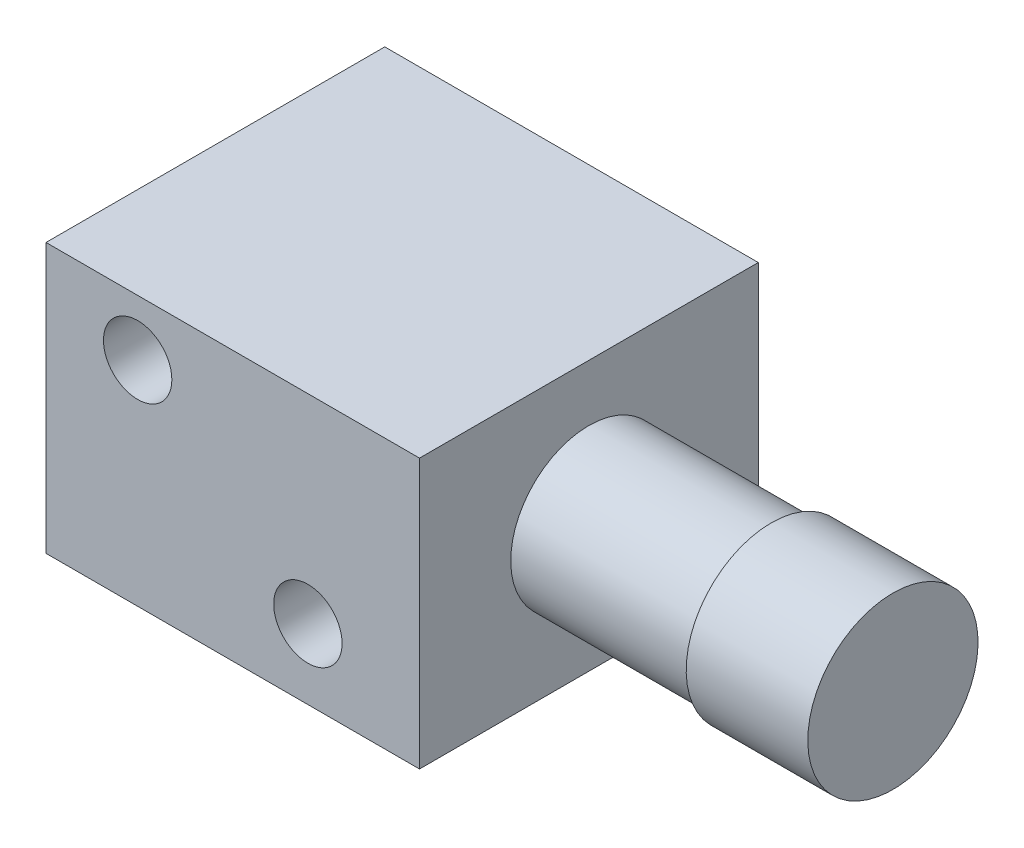
SolidWorks part; units mm, degrees
ref_plane "Front Plane" through (0, 0, 0) normal (0, 0, 1) x (1, 0, 0)
ref_plane "Top Plane" through (0, 0, 0) normal (0, 1, 0) x (1, 0, 0)
ref_plane "Right Plane" through (0, 0, 0) normal (1, 0, 0) x (0, 0, -1)
sketch "Sketch1" plane through (0, 0, 0) normal (0, 0, 1) x (1, 0, 0)
  line L1 (-5.461, 3.937) -> (5.461, 3.937)
  line L2 (-5.461, 3.937) -> (-5.461, -3.937)
  line L3 (-5.461, -3.937) -> (5.461, -3.937)
  line L4 (5.461, 3.937) -> (5.461, -3.937)
  line L5 (-5.461, 3.937) -> (5.461, -3.937) construction
  line L6 (-5.461, -3.937) -> (5.461, 3.937) construction
  point P0 (0, 0)
  dimension "D1" = 7.874
  dimension "D2" = 10.922
extrude "Boss-Extrude1" add sketch "Sketch1" along normal blind 9.906
sketch "Sketch2" plane through (5.461, 0, 0) normal (1, 0, 0) x (0, 0, -1)
  line L0 (0, 0) -> (-9.906, 0) construction
  line L1 (-9.906, -3.937) -> (-9.906, 3.937) construction
  line L2 (-4.953, 3.937) -> (-4.953, -3.937) construction
  line L3 (-9.906, 3.937) -> (0, 3.937) construction
  line L4 (-9.906, -3.937) -> (0, -3.937) construction
  circle A0 centre (-4.953, 0) radius 2.286
  dimension "D1" = 4.572
extrude "Boss-Extrude2" add sketch "Sketch2" along normal blind 5.334
sketch "Sketch3" plane through (10.795, 0, 0) normal (1, 0, 0) x (0, 0, -1)
  circle A0 centre (-4.953, 0) radius 2.4892
  dimension "D1" = 4.9784
extrude "Boss-Extrude3" add sketch "Sketch3" along normal blind 3.556
sketch "Sketch4" plane through (-5.461, 0, 0) normal (-1, 0, 0) x (0, 0, 1)
  line L0 (0, 0) -> (9.906, 0) construction
  line L1 (0, 3.937) -> (0, -3.937) construction
  line L2 (9.906, 3.937) -> (9.906, -3.937) construction
  line L3 (4.953, 3.937) -> (4.953, -3.937) construction
  line L4 (9.906, 3.937) -> (0, 3.937) construction
  line L5 (9.906, -3.937) -> (0, -3.937) construction
  circle A0 centre (4.953, 0) radius 1.524
  dimension "D1" = 3.048
extrude "Boss-Extrude4" add sketch "Sketch4" along normal blind 1.905
sketch "Sketch5" plane through (0, 0, 9.906) normal (0, 0, 1) x (1, 0, 0)
  circle A0 centre (-2.7811, 2.3005) radius 1
  circle A1 centre (2.1973, -1.8905) radius 1
  point P4 (0, 0)
  dimension "D1" = 2
  dimension "D2" = 2
  dimension "D4" = 4.191
  dimension "D3" = 4.9784
extrude "Cut-Extrude1" cut sketch "Sketch5" against normal blind 3.81 contours A1 | A0
sketch "Sketch6" plane through (0, 0, 0) normal (1, 0, 0) x (0, 0, -1)
  circle A0 centre (-4.953, 0) radius 2.4892 construction
  point P0 (-4.953, -2.4892)
ref_plane "Plane1" through (0, -2.4892, 0) normal (0, 1, 0) x (1, 0, 0)
sketch "Sketch7" plane through (0, -2.4892, 0) normal (0, 1, 0) x (1, 0, 0)
  line L0 (14.351, -4.953) -> (10.795, -4.953) construction
  line L1 (14.351, -7.4422) -> (14.351, -2.4638) construction
  line L2 (10.795, -2.4638) -> (10.795, -7.4422) construction
  line L3 (12.573, -7.4422) -> (12.573, -2.4638) construction
  line L4 (10.795, -7.4422) -> (14.351, -7.4422) construction
  line L5 (14.351, -2.4638) -> (10.795, -2.4638) construction
  circle A0 centre (12.573, -4.953) radius 0.889
  dimension "D1" = 1.778
extrude "Cut-Extrude2" cut sketch "Sketch7" along normal blind 3.81
sketch "Sketch8" plane through (0, 0, 0) normal (0, 0, 1) x (1, 0, 0)
  line L0 (-5.461, 3.937) -> (-5.461, -3.937) construction
  line L1 (-5.461, 0.635) -> (-6.6822, 0.635)
  line L2 (-5.461, 0.635) -> (-5.461, -0.635)
  line L3 (-5.461, -0.635) -> (-6.6822, -0.635)
  line L4 (-6.6822, 0.635) -> (-6.6822, -0.635)
  line L5 (0, 0) -> (-3.3125, 0) construction
  dimension "D1" = 1.27
extrude "Boss-Extrude5" add sketch "Sketch8" along normal blind 0.254
